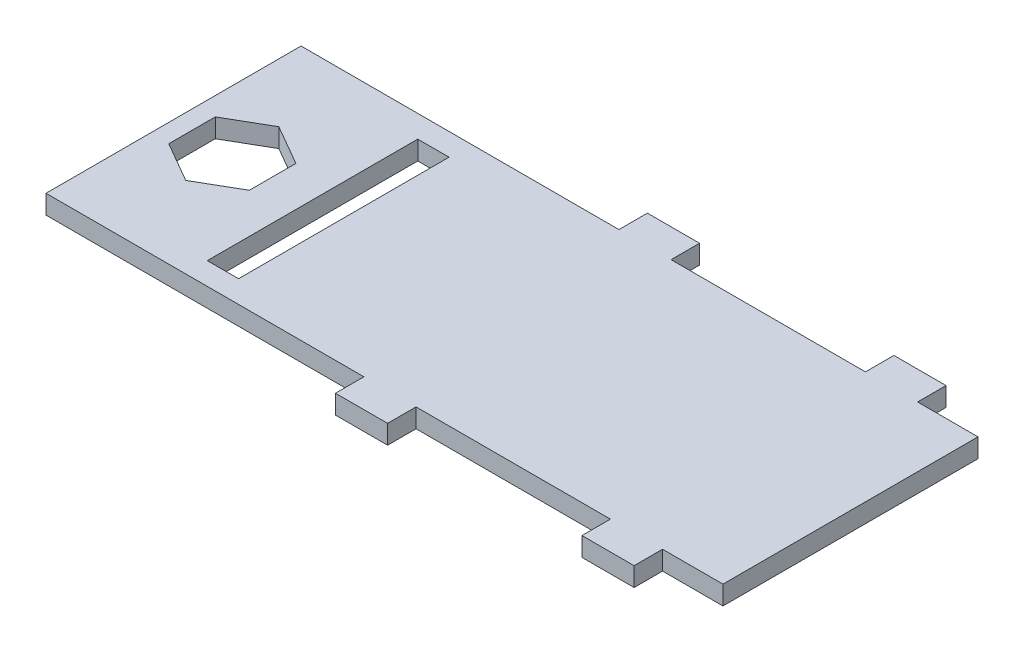
SolidWorks part; units mm, degrees
ref_plane "Front Plane" through (0, 0, 0) normal (0, 0, 1) x (1, 0, 0)
ref_plane "Top Plane" through (0, 0, 0) normal (0, 1, 0) x (1, 0, 0)
ref_plane "Right Plane" through (0, 0, 0) normal (1, 0, 0) x (0, 0, -1)
sketch "Sketch1" plane through (0, 0, 0) normal (0, 1, 0) x (1, 0, 0)
  line L1 (-50.7984, -5.3305) -> (-15.0984, -5.3305)
  line L2 (-50.7984, -5.3305) -> (-50.7984, -18.7805)
  line L3 (-50.7984, -18.7805) -> (-15.0984, -18.7805)
  line L4 (-15.0984, -5.3305) -> (-15.0984, -18.7805)
  dimension "D1" = 13.45
  dimension "D2" = 35.7
sketch "Sketch2" plane through (0, 0, 0) normal (0, 1, 0) x (1, 0, 0)
  line L0 (-50.7984, -5.3305) -> (-15.0984, -5.3305) construction
  line L1 (-34.0334, -5.3305) -> (-31.2834, -5.3305)
  line L2 (-34.0334, -5.3305) -> (-34.0334, -3.8305)
  line L3 (-34.0334, -3.8305) -> (-31.2834, -3.8305)
  line L4 (-31.2834, -5.3305) -> (-31.2834, -3.8305)
  line L5 (-50.7984, -5.3305) -> (-50.7984, -18.7805) construction
  line L6 (-15.0984, -5.3305) -> (-15.0984, -18.7805) construction
  line L7 (-50.7984, -18.7805) -> (-15.0984, -18.7805) construction
  line L8 (-34.0334, -18.7805) -> (-31.2834, -18.7805)
  line L9 (-34.0334, -18.7805) -> (-34.0334, -20.2805)
  line L10 (-34.0334, -20.2805) -> (-31.2834, -20.2805)
  line L11 (-31.2834, -18.7805) -> (-31.2834, -20.2805)
  line L12 (-21.0334, -5.3305) -> (-21.0334, -3.8305)
  line L13 (-21.0334, -3.8305) -> (-18.2834, -3.8305)
  line L14 (-18.2834, -5.3305) -> (-18.2834, -3.8305)
  line L15 (-21.0334, -5.3305) -> (-18.2834, -5.3305)
  line L16 (-21.0334, -18.7805) -> (-18.2834, -18.7805)
  line L17 (-18.2834, -18.7805) -> (-18.2834, -20.2805)
  line L18 (-21.0334, -20.2805) -> (-18.2834, -20.2805)
  line L19 (-21.0334, -18.7805) -> (-21.0334, -20.2805)
  dimension "D1" = 2.75
  dimension "D2" = 16.765
  dimension "D3" = 16.185
  dimension "D4" = 1.5
  dimension "D5" = 1.5
  dimension "D6" = 2.75
  dimension "D7" = 16.765
  dimension "D8" = 2
extrude "Boss-Extrude1" add sketch "Sketch1" along normal blind 1
extrude "Boss-Extrude2" add sketch "Sketch2" along normal blind 1
sketch "Sketch3" plane through (0, 0, 0) normal (0, -1, 0) x (-1, 0, 0)
  line L0 (50.7984, -18.7805) -> (15.0984, -18.7805) construction
  line L1 (43.4684, -17.6055) -> (41.8184, -17.6055)
  line L2 (43.4684, -17.6055) -> (43.4684, -6.5055)
  line L3 (43.4684, -6.5055) -> (41.8184, -6.5055)
  line L4 (41.8184, -17.6055) -> (41.8184, -6.5055)
  line L5 (50.7984, -5.3305) -> (15.0984, -5.3305) construction
  line L6 (50.7984, -5.3305) -> (50.7984, -18.7805) construction
  dimension "D1" = 1.65
  dimension "D2" = 11.1
  dimension "D3" = 1.175
  dimension "D4" = 1.175
  dimension "D5" = 7.33
extrude "adapter_PCB_hole" cut sketch "Sketch3" against normal blind 1
sketch "Sketch4" plane through (0, 0, 0) normal (0, -1, 0) x (-1, 0, 0)
  line L0 (50.7984, -18.7805) -> (15.0984, -18.7805) construction
  line L1 (49.8234, -13.2823) -> (49.8234, -10.8286)
  line L2 (49.8234, -10.8286) -> (47.6984, -9.6017)
  line L3 (47.6984, -9.6017) -> (45.5734, -10.8286)
  line L4 (45.5734, -10.8286) -> (45.5734, -13.2823)
  line L5 (45.5734, -13.2823) -> (47.6984, -14.5092)
  line L6 (47.6984, -14.5092) -> (49.8234, -13.2823)
  line L7 (50.7984, -5.3305) -> (15.0984, -5.3305) construction
  line L8 (50.7984, -5.3305) -> (50.7984, -18.7805) construction
  circle A0 centre (47.6984, -12.0555) radius 2.125 construction
  dimension "D1" = 6.725
  dimension "D2" = 6.725
  dimension "D3" = 3.1
extrude "Cut-Extrude2" cut sketch "Sketch4" against normal blind 1
